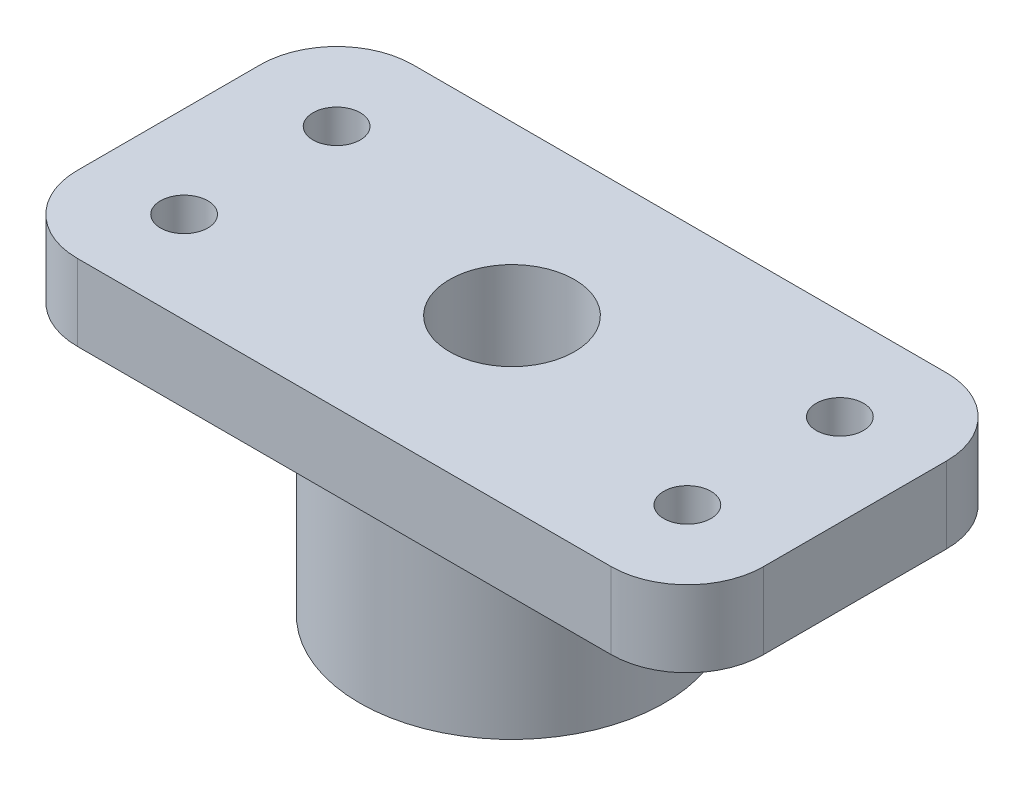
SolidWorks part; units mm, degrees
ref_plane "Alzado" through (0, 0, 0) normal (0, 0, 1) x (1, 0, 0)
ref_plane "Planta" through (0, 0, 0) normal (0, 1, 0) x (1, 0, 0)
ref_plane "Vista lateral" through (0, 0, 0) normal (1, 0, 0) x (0, 0, -1)
sketch "Croquis1" plane through (0, 0, 0) normal (0, 1, 0) x (1, 0, 0)
  circle A0 centre (0, 0) radius 10
  circle A1 centre (0, 0) radius 3.5
  dimension "D1" = 20
  dimension "D2" = 7
extrude "Extruir1" add sketch "Croquis1" along normal blind 12
sketch "Croquis2" plane through (0, 12, 0) normal (0, 1, 0) x (1, 0, 0)
  line L1 (22.5, 11) -> (-22.5, 11)
  line L2 (22.5, 11) -> (22.5, -11)
  line L3 (22.5, -11) -> (-22.5, -11)
  line L4 (-22.5, 11) -> (-22.5, -11)
  line L5 (22.5, 11) -> (-22.5, -11) construction
  line L6 (22.5, -11) -> (-22.5, 11) construction
  point P0 (0, 0)
  dimension "D1" = 45
  dimension "D2" = 22
extrude "Saliente-Extruir1" add sketch "Croquis2" along normal blind 5
fillet "Redondeo1" radius 5 1 edges at (22.5, 14.5, -11)
fillet "Redondeo2" radius 5 1 edges at (22.5, 14.5, 11)
fillet "Redondeo3" radius 5 1 edges at (-22.5, 14.5, 11)
fillet "Redondeo4" radius 5 1 edges at (-22.5, 14.5, -11)
sketch "Croquis3" plane through (0, 0, 0) normal (0, -1, 0) x (1, 0, 0)
  circle A0 centre (0, 0) radius 4.1
  dimension "D1" = 8.2
extrude "Cortar-Extruir1" cut sketch "Croquis3" against normal blind 45
sketch "Croquis4" plane through (0, 12, 0) normal (0, -1, 0) x (1, 0, 0)
  circle A0 centre (-16.5, 5) radius 1.55
  circle A1 centre (-16.5, -5) radius 1.55
  circle A2 centre (16.5, 5) radius 1.55
  circle A3 centre (16.5, -5) radius 1.55
extrude "Cortar-Extruir2" cut sketch "Croquis4" against normal blind 45
